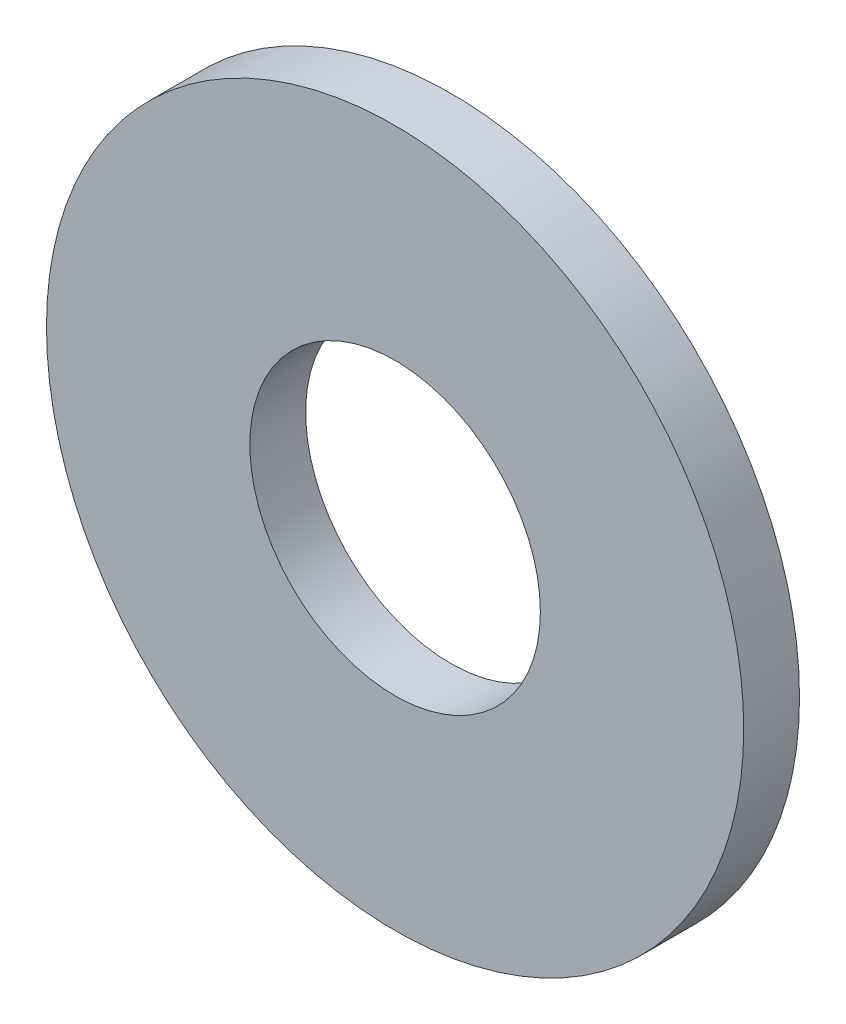
SolidWorks part; units mm, degrees
ref_plane "Front Plane" through (0, 0, 0) normal (0, 0, 1) x (1, 0, 0)
ref_plane "Top Plane" through (0, 0, 0) normal (0, 1, 0) x (1, 0, 0)
ref_plane "Right Plane" through (0, 0, 0) normal (1, 0, 0) x (0, 0, -1)
sketch "Sketch1" plane through (0, 0, 0) normal (0, 0, 1) x (1, 0, 0)
  circle A0 centre (0, 0) radius 1.9844
  circle A1 centre (0, 0) radius 4.7625
  dimension "ID" = 3.9688
  dimension "OD" = 9.525
extrude "Extrude1" add sketch "Sketch1" against normal blind 0.762
